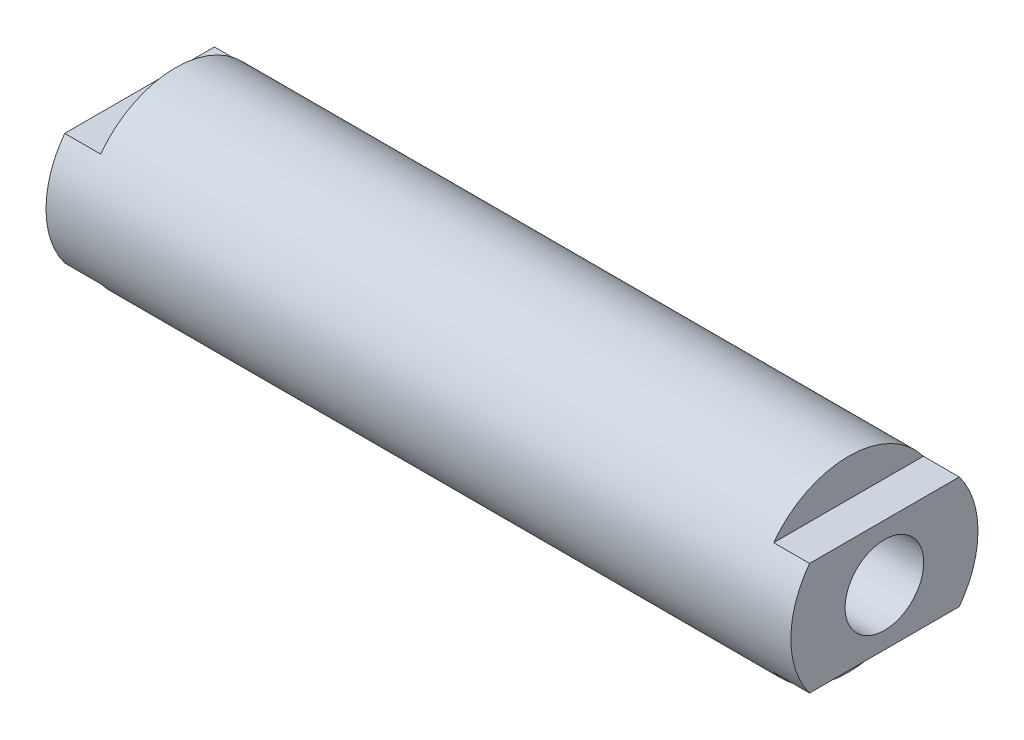
SolidWorks part; units mm, degrees
ref_plane "Plan de face" through (0, 0, 0) normal (0, 0, 1) x (1, 0, 0)
ref_plane "Plan de dessus" through (0, 0, 0) normal (0, 1, 0) x (1, 0, 0)
ref_plane "Plan de droite" through (0, 0, 0) normal (1, 0, 0) x (0, 0, -1)
sketch "Esquisse1" plane through (0, 0, 0) normal (0, 0, 1) x (1, 0, 0)
  line L0 (-69.4577, 0) -> (86.7621, 0) construction
  line L2 (-49.75, 0) -> (49.75, 0)
  line L3 (-49.75, 0) -> (-49.75, 12.5)
  line L4 (-49.75, 12.5) -> (49.75, 12.5)
  line L5 (49.75, 0) -> (49.75, 12.5)
  dimension "D1" = 99.5
  dimension "D2" = 12.5
revolve "Révolution1" add sketch "Esquisse1" angle 360 about L0
sketch "Esquisse2" plane through (0, 0, 0) normal (0, 0, 1) x (1, 0, 0)
  line L1 (-49.75, 12.5) -> (-44.95, 12.5)
  line L2 (-49.75, 12.5) -> (-49.75, 7.5)
  line L3 (-49.75, 7.5) -> (-44.95, 7.5)
  line L4 (-44.95, 12.5) -> (-44.95, 7.5)
  dimension "D1" = 4.8
  dimension "D2" = 7.5
extrude "Enlèv. mat.-Extru.1" cut sketch "Esquisse2" against normal through all both and the other way through all
mirror "Symétrie1" about plane through (0, 0, 0) normal (0, 1, 0) of "Enlèv. mat.-Extru.1"
hole_wizard "Diamètre du perçage Ø10.5 (10.5)1" positions "Esquisse4" profile "Esquisse5" hole size "Ø10.5" standard "DIN"
sketch "Esquisse4" plane through (-49.75, 0, 0) normal (-1, 0, 0) x (0, 0, 1)
  point P0 (0, 0)
sketch "Esquisse5" plane through (-49.75, 0, 0) normal (0, 1, 0) x (0, 0, 1)
  line L0 (0, 0) -> (0, 36.1545)
  line L1 (0, 36.1545) -> (5.25, 33)
  line L2 (5.25, 33) -> (5.25, 0)
  line L5 (5.25, 0) -> (0, 0)
  line L10 (0, 36.1545) -> (-5.25, 33) construction
  line L11 (0, -6.35) -> (0, 107.95) construction
  dimension "Diamètre du perçage" = 10.5
  dimension "Profondeur du perçage" = 33
  dimension "Angle de pointe" = 118
mirror "Symétrie2" about plane through (0, 0, 0) normal (1, 0, 0) of "Diamètre du perçage Ø10.5 (10.5)1", "Symétrie1", "Enlèv. mat.-Extru.1"
